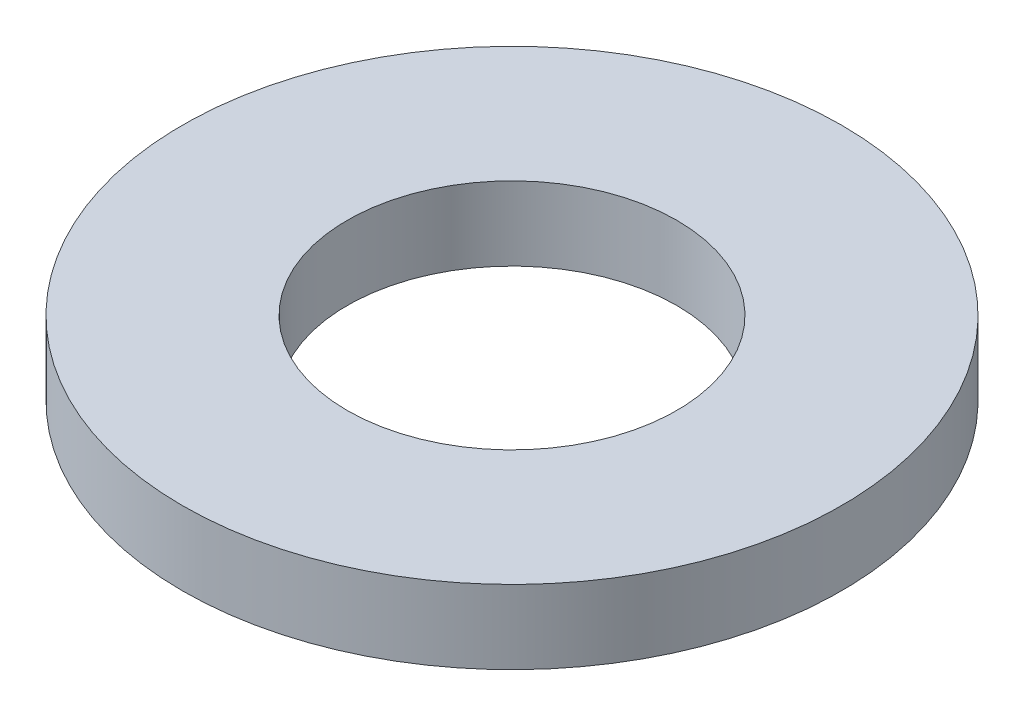
SolidWorks part; units mm, degrees
material "AISI 304"
ref_plane "Front Plane" through (0, 0, 0) normal (0, 0, 1) x (1, 0, 0)
ref_plane "Top Plane" through (0, 0, 0) normal (0, 1, 0) x (1, 0, 0)
ref_plane "Right Plane" through (0, 0, 0) normal (1, 0, 0) x (0, 0, -1)
sketch "Sketch1" plane through (0, 0, 0) normal (0, 1, 0) x (1, 0, 0)
  circle A0 centre (0, 0) radius 3.175
  dimension "OD" = 6.35
extrude "Boss-Extrude1" add sketch "Sketch1" along normal blind 0.7112
sketch "Sketch5" plane through (0, 0.7112, 0) normal (0, 1, 0) x (-1, 0, 0)
  circle A0 centre (0, 0) radius 1.5875
  dimension "ID" = 3.175
extrude "Cut-Extrude1" cut sketch "Sketch5" against normal through all
